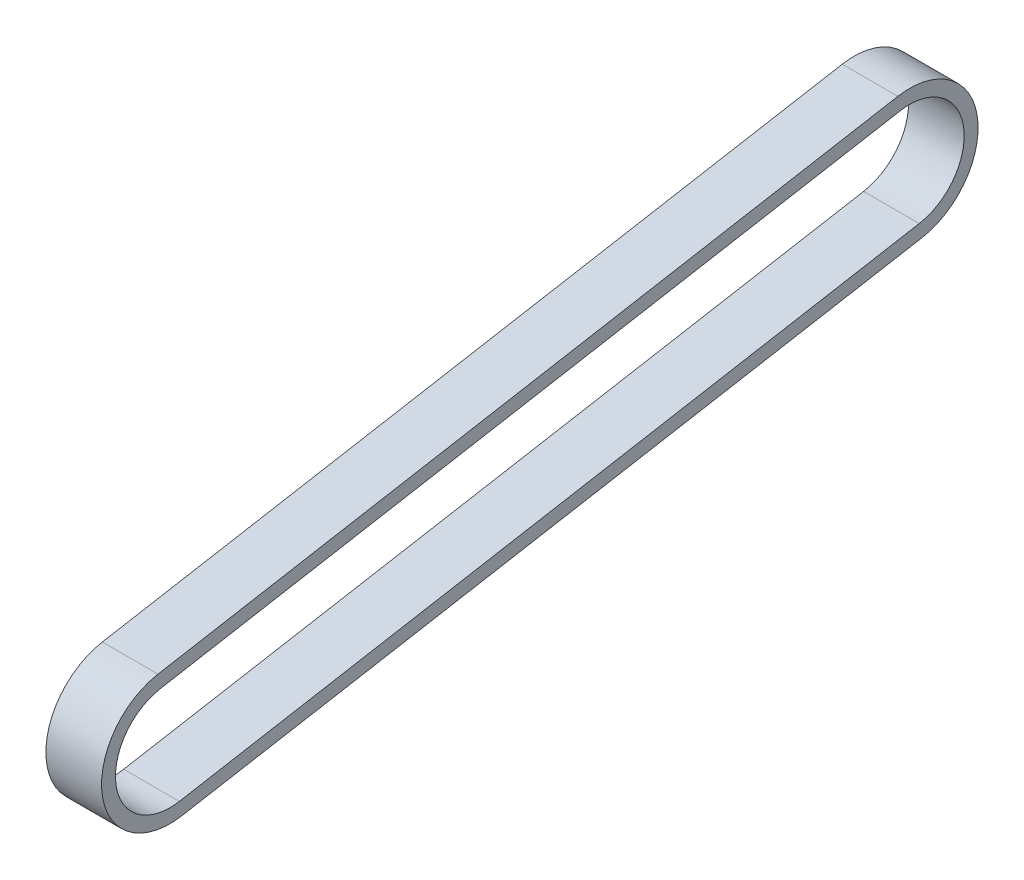
SolidWorks part; units mm, degrees
material "Rubber"
ref_plane "Front Plane" through (0, 0, 0) normal (0, 0, 1) x (1, 0, 0)
ref_plane "Top Plane" through (0, 0, 0) normal (0, 1, 0) x (1, 0, 0)
ref_plane "Right Plane" through (0, 0, 0) normal (1, 0, 0) x (0, 0, -1)
ref_plane "Plane2" through (-30.95, 0, 0) normal (-1, 0, 0) x (0, 0, 1)
ref_plane "Plane3" through (-37.95, 0, 0) normal (1, 0, 0) x (0, 0, -1)
ref_plane "Plane4" through (-34.45, 0, 0) normal (-1, 0, 0) x (0, 0, 1)
sketch "Sketch2" plane through (-34.45, 0, 0) normal (-1, 0, 0) x (0, 0, 1)
  line L0 (-40, 70) -> (39.7694, 55.9345) construction
  line L1 (-40, 70) -> (39.7694, 55.9345)
  line L2 (-40, 70) -> (39.7694, 55.9345) construction
  line L3 (-38.8946, 76.2693) -> (40.8749, 62.2038) construction
  line L4 (-41.1054, 63.7307) -> (38.664, 49.6652) construction
  line L5 (-38.7209, 77.2541) -> (41.0485, 63.1886)
  line L6 (-41.2791, 62.7459) -> (38.4903, 48.6804)
  line L7 (-38.9814, 75.7769) -> (40.788, 61.7114)
  line L8 (-41.0186, 64.2231) -> (38.7508, 50.1576)
  arc A0 (-38.8946, 76.2693) -> (-41.1054, 63.7307) centre (-40, 70) ccw construction
  arc A1 (38.664, 49.6652) -> (40.8749, 62.2038) centre (39.7694, 55.9345) ccw construction
  arc A2 (38.4903, 48.6804) -> (41.0485, 63.1886) centre (39.7694, 55.9345) ccw
  arc A3 (-38.7209, 77.2541) -> (-41.2791, 62.7459) centre (-40, 70) ccw
  arc A4 (38.7508, 50.1576) -> (40.788, 61.7114) centre (39.7694, 55.9345) ccw
  arc A5 (-38.9814, 75.7769) -> (-41.0186, 64.2231) centre (-40, 70) ccw
  point P2 (-0.1153, 62.9672)
  dimension "D3" = 12.732
  dimension "D1" = 1
  dimension "D2" = 0.5
extrude "Boss-Extrude1" add sketch "Sketch2" along normal mid plane 6
